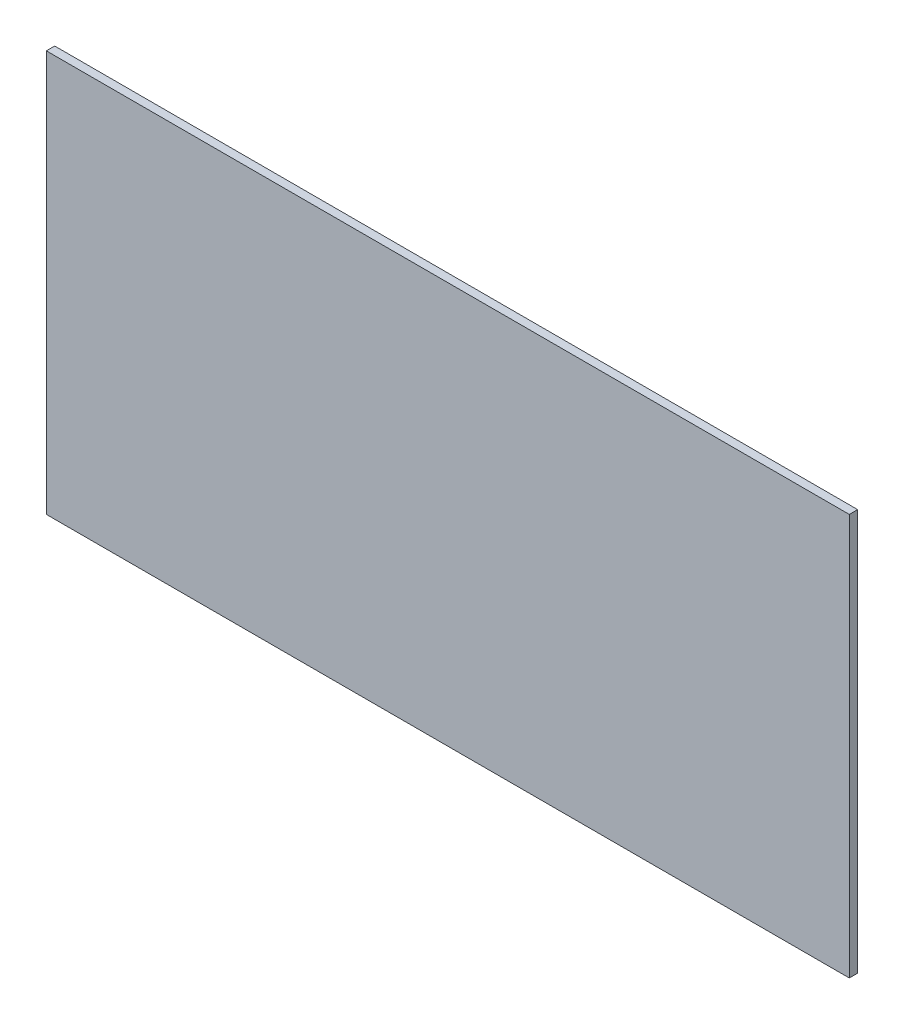
SolidWorks part; units mm, degrees
ref_plane "Front Plane" through (0, 0, 0) normal (0, 0, 1) x (1, 0, 0)
ref_plane "Top Plane" through (0, 0, 0) normal (0, 1, 0) x (1, 0, 0)
ref_plane "Right Plane" through (0, 0, 0) normal (1, 0, 0) x (0, 0, -1)
sketch "Sketch1" plane through (0, 0, 0) normal (0, 0, 1) x (1, 0, 0)
  line L1 (0, 0) -> (2438.4, 0)
  line L2 (0, 0) -> (0, -1219.2)
  line L3 (0, -1219.2) -> (2438.4, -1219.2)
  line L4 (2438.4, 0) -> (2438.4, -1219.2)
  dimension "D1" = 2438.4
  dimension "D2" = 1219.2
extrude "Boss-Extrude1" add sketch "Sketch1" along normal blind 25.4
